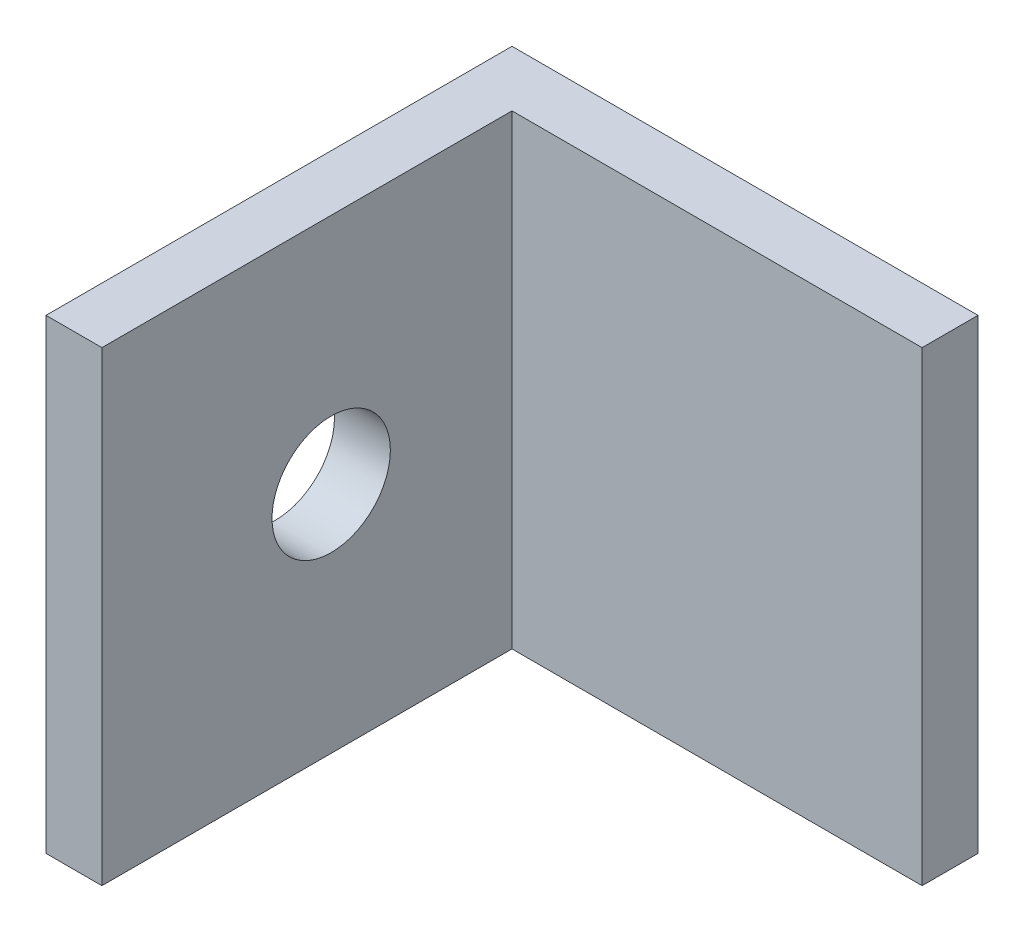
SolidWorks part; units mm, degrees
ref_plane "Front Plane" through (0, 0, 0) normal (0, 0, 1) x (1, 0, 0)
ref_plane "Top Plane" through (0, 0, 0) normal (0, 1, 0) x (1, 0, 0)
ref_plane "Right Plane" through (0, 0, 0) normal (1, 0, 0) x (0, 0, -1)
sketch "Sketch1" plane through (0, 0, 0) normal (0, 1, 0) x (1, 0, 0)
  line L1 (0, 0) -> (3, 0)
  line L2 (0, 0) -> (0, -25)
  line L3 (0, -25) -> (3, -25)
  line L4 (3, -3) -> (3, -25)
  line L5 (0, 0) -> (25, 0)
  line L6 (0, 0) -> (0, -3)
  line L7 (3, -3) -> (25, -3)
  line L8 (25, 0) -> (25, -3)
  dimension "D1" = 25
  dimension "D2" = 25
  dimension "D3" = 3
  dimension "D4" = 3
extrude "Boss-Extrude1" add sketch "Sketch1" along normal blind 25 contours L8 L5 L1 L2 L3 L4 L7
sketch "Sketch2" plane through (3, 0, 0) normal (1, 0, 0) x (0, 0, -1)
  line L1 (-3, 25) -> (-25, 25) construction
  line L2 (0, 25) -> (0, 0) construction
  circle A0 centre (-12.7, 12.5) radius 3.175
  dimension "D1" = 6.35
  dimension "D2" = 12.7
  dimension "D3" = 12.5
extrude "Cut-Extrude1" cut sketch "Sketch2" against normal through all
